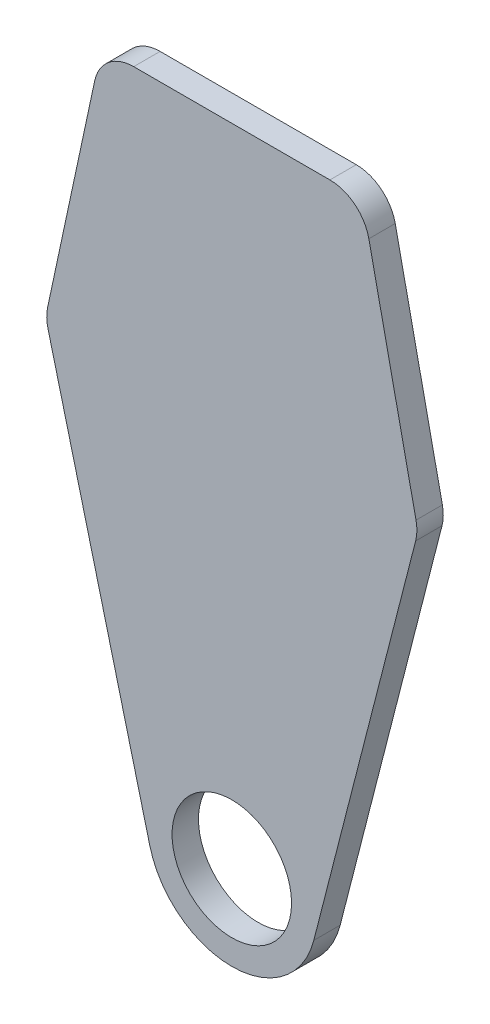
SolidWorks part; units mm, degrees
material "6061-T6 (SS)"
ref_plane "Front Plane" through (0, 0, 0) normal (0, 0, 1) x (1, 0, 0)
ref_plane "Top Plane" through (0, 0, 0) normal (0, 1, 0) x (1, 0, 0)
ref_plane "Right Plane" through (0, 0, 0) normal (1, 0, 0) x (0, 0, -1)
sketch "Sketch1" plane through (0, 0, 0) normal (0, 0, 1) x (1, 0, 0)
  line L0 (680.1598, 1427.7413) -> (2856.1598, 1427.7413) construction
  line L1 (-33.2359, 164.6767) -> (33.2359, 164.6767)
  line L2 (-33.2359, 164.6767) -> (-47.4853, 98.171)
  line L3 (-47.4853, 98.171) -> (47.4853, 98.171) construction
  line L4 (-47.4853, 98.171) -> (-20.9122, -5.3671)
  line L5 (33.2359, 164.6767) -> (47.4853, 98.171)
  line L6 (47.4853, 98.171) -> (20.9122, -5.3671)
  circle A0 centre (0, 0) radius 15.24
  arc A1 (-20.9122, -5.3671) -> (20.9122, -5.3671) centre (0, 0) ccw
  point P8 (0, 164.6767)
  point P9 (0, 98.171)
  dimension "D1" = 30.48
  dimension "D2" = 43.18
  dimension "D3" = 164.6767
  dimension "D4" = 98.171
  dimension "D5" = 94.9706
  dimension "D6" = 66.4718
extrude "Boss-Extrude1" add sketch "Sketch1" along normal blind 6.731 contours A0 | L2 L4 A1 L6 L5 L1
fillet "Fillet1" radius 10.16 2 edges at (-47.4853, 98.171, 3.3655) (47.4853, 98.171, 3.3655)
fillet "Fillet2" radius 10.16 2 edges at (-33.2359, 164.6767, 3.3655) (33.2359, 164.6767, 3.3655)
